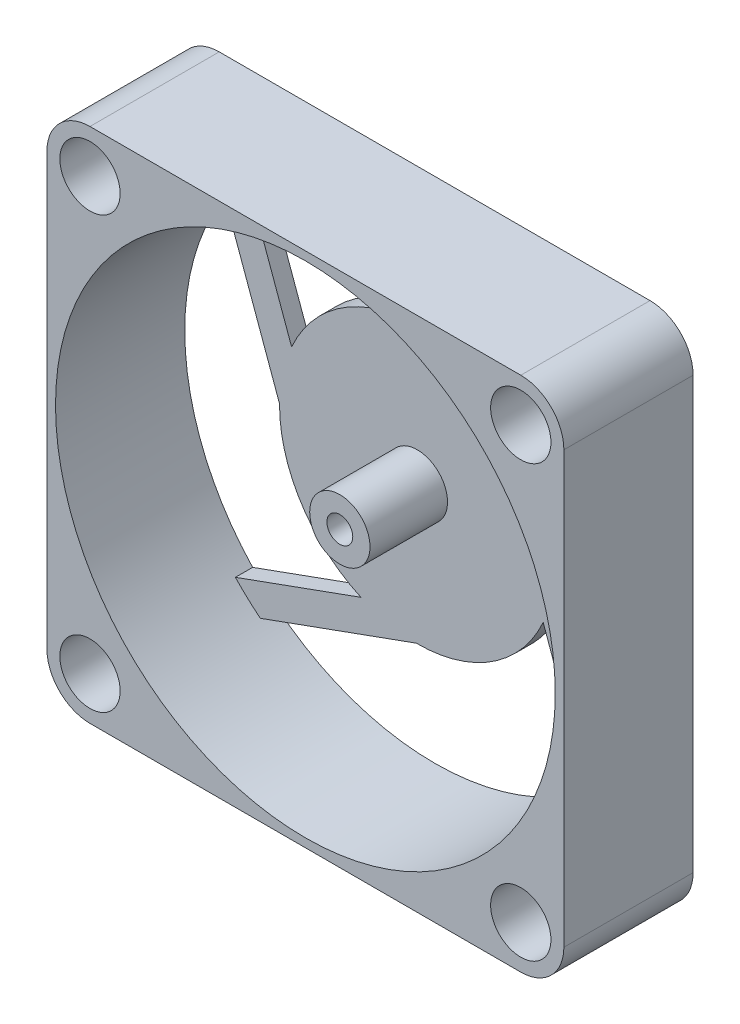
SolidWorks part; units mm, degrees
ref_plane "Plano frontal" through (0, 0, 0) normal (0, 0, 1) x (1, 0, 0)
ref_plane "Plano superior" through (0, 0, 0) normal (0, 1, 0) x (1, 0, 0)
ref_plane "Plano direito" through (0, 0, 0) normal (1, 0, 0) x (0, 0, -1)
sketch "Esboço1" plane through (0, 0, 0) normal (0, 0, 1) x (1, 0, 0)
  line L0 (0, 60) -> (60, 0) construction
  line L1 (0, 0) -> (60, 0)
  line L2 (0, 0) -> (0, 60)
  line L3 (0, 60) -> (60, 60)
  line L4 (60, 0) -> (60, 60)
  circle A0 centre (30, 30) radius 29
  dimension "D2" = 58
  dimension "D1" = 60
extrude "Ressalto-extrusão1" add sketch "Esboço1" along normal blind 15
sketch "Esboço2" plane through (0, 0, 15) normal (0, 0, 1) x (1, 0, 0)
  line L1 (55, 5) -> (5, 5) construction
  line L2 (55, 5) -> (55, 55) construction
  line L3 (55, 55) -> (5, 55) construction
  line L4 (5, 5) -> (5, 55) construction
  line L5 (55, 5) -> (5, 55) construction
  line L6 (55, 55) -> (5, 5) construction
  circle A0 centre (5, 55) radius 2
  circle A1 centre (55, 55) radius 2
  circle A2 centre (55, 5) radius 2
  circle A3 centre (5, 5) radius 2
  point P0 (30, 30)
  dimension "D2" = 4
  dimension "D1" = 50
extrude "Corte-extrusão1" cut sketch "Esboço2" against normal blind 15
sketch "Esboço3" plane through (0, 0, 15) normal (0, 0, 1) x (1, 0, 0)
  circle A0 centre (5, 55) radius 3.5
  circle A1 centre (55, 55) radius 3.5
  circle A2 centre (55, 5) radius 3.5
  circle A3 centre (5, 5) radius 3.5
  dimension "D1" = 7
extrude "Corte-extrusão2" cut sketch "Esboço3" against normal blind 5
fillet "Filete1" radius 5 4 edges at (60, 0, 7.5) (60, 60, 7.5) (0, 0, 7.5) (0, 60, 7.5)
sketch "Esboço4" plane through (0, 0, 0) normal (0, 0, -1) x (-1, 0, 0)
  line L0 (-30, 59) -> (-30, 1) construction
  line L1 (-55, 55) -> (-30.1308, 45.9995)
  line L2 (-55, 5) -> (-45.9995, 29.8692)
  line L3 (-5, 55) -> (-14.0005, 30.1308)
  line L4 (-5, 5) -> (-29.8692, 14.0005)
  line L5 (-56.1911, 51.7089) -> (-36.5467, 44.5993)
  line L6 (-51.7089, 3.8089) -> (-44.5993, 23.4533)
  line L7 (-3.8089, 8.2911) -> (-23.4533, 15.4007)
  line L8 (-8.2911, 56.1911) -> (-15.4007, 36.5467)
  line L9 (-51.7089, 3.8089) -> (-40.8136, 33.9136) construction
  line L10 (-55, 5) -> (-44.1047, 35.1047) construction
  line L11 (-5, 55) -> (-15.8953, 24.8953) construction
  line L12 (-3.8089, 8.2911) -> (-33.9136, 19.1864) construction
  line L13 (-5, 5) -> (-35.1047, 15.8953) construction
  line L14 (-8.2911, 56.1911) -> (-19.1864, 26.0864) construction
  line L15 (-55, 55) -> (-24.8953, 44.1047) construction
  line L16 (-56.1911, 51.7089) -> (-26.0864, 40.8136) construction
  circle A0 centre (-30, 30) radius 15 construction
  circle A1 centre (-30, 30) radius 29 construction
  arc A2 (-44.5993, 23.4533) -> (-29.8692, 14.0005) centre (-30, 30) ccw
  circle A3 centre (-30, 30) radius 16 construction
  arc A4 (-23.4533, 15.4007) -> (-14.0005, 30.1308) centre (-30, 30) ccw
  arc A5 (-15.4007, 36.5467) -> (-30.1308, 45.9995) centre (-30, 30) ccw
  arc A6 (-36.5467, 44.5993) -> (-45.9995, 29.8692) centre (-30, 30) ccw
  circle A7 centre (-30, 30) radius 29
  circle M15 centre (-30, 30) radius 29
  dimension "D1" = 30
  dimension "D2" = 1
  dimension "D3" = 3.5
extrude "Ressalto-extrusão2" add sketch "Esboço4" against normal blind 2 contours L5 A6 L2 L6 A2 L4 L7 A4 L3 L8 A5 L1 M15
sketch "Esboço5" plane through (0, 0, 2) normal (0, 0, 1) x (1, 0, 0)
  circle A0 centre (30, 30) radius 3.5
  dimension "D1" = 7
extrude "Ressalto-extrusão3" add sketch "Esboço5" along normal blind 9
sketch "Esboço6" plane through (0, 0, 11) normal (0, 0, 1) x (1, 0, 0)
  circle A0 centre (30, 30) radius 1.5
  dimension "D1" = 3
extrude "Corte-extrusão3" cut sketch "Esboço6" against normal blind 18.3
sketch "Esboço7" plane through (0, 0, 0) normal (0, 0, -1) x (-1, 0, 0)
  circle A0 centre (-30, 30) radius 2.5
  dimension "D1" = 5
extrude "Corte-extrusão4" cut sketch "Esboço7" against normal blind 1.5
